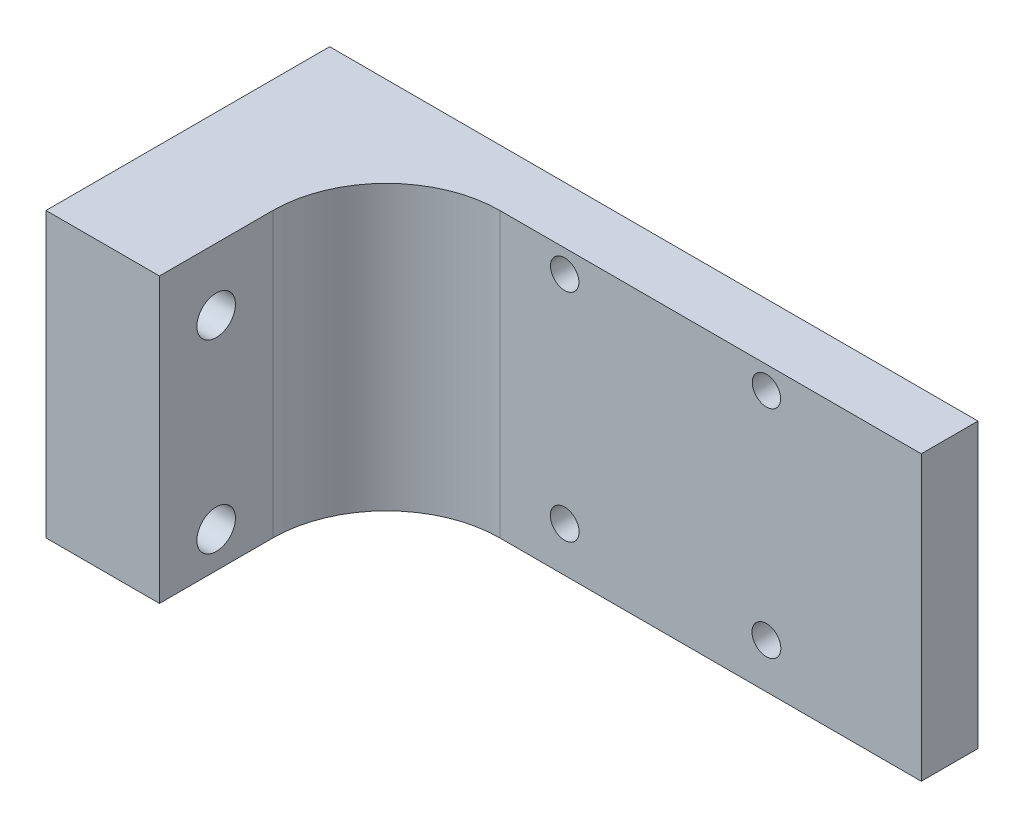
SolidWorks part; units mm, degrees
ref_plane "Front Plane" through (0, 0, 0) normal (0, 0, 1) x (1, 0, 0)
ref_plane "Top Plane" through (0, 0, 0) normal (0, 1, 0) x (1, 0, 0)
ref_plane "Right Plane" through (0, 0, 0) normal (1, 0, 0) x (0, 0, -1)
sketch "Sketch1" plane through (0, 0, 0) normal (0, 0, 1) x (1, 0, 0)
  line L1 (0, 0) -> (57.15, 0)
  line L2 (0, 0) -> (0, -25)
  line L3 (0, -25) -> (57.15, -25)
  line L4 (57.15, 0) -> (57.15, -25)
  dimension "D1" = 57.15
  dimension "D2" = 25
extrude "Boss-Extrude1" add sketch "Sketch1" along normal blind 5
sketch "Sketch2" plane through (0, 0, 5) normal (0, 0, 1) x (1, 0, 0)
  line L0 (0, -2) -> (57.15, -2) construction
  line L1 (0, 0) -> (0, -25) construction
  line L2 (57.15, -25) -> (57.15, 0) construction
  line L3 (37.15, -25) -> (37.15, 0) construction
  line L4 (25.72, -2) -> (25.72, -25) construction
  line L5 (43.5, -2) -> (43.5, -25) construction
  line L6 (17.15, -25) -> (17.15, 0) construction
  line L7 (0, -25) -> (57.15, -25) construction
  line L8 (57.15, 0) -> (0, 0) construction
  line L9 (57.15, -25) -> (57.15, 0) construction
  circle A2 centre (25.72, -2) radius 1.25
  circle A3 centre (43.5, -2) radius 1.25
  circle A4 centre (25.72, -21.05) radius 1.27
  circle A5 centre (43.5, -21.05) radius 1.27
  dimension "D3" = 11.43
  dimension "D4" = 6.35
  dimension "D2" = 20
  dimension "D7" = 2.5
  dimension "D8" = 2.54
  dimension "D9" = 19.05
  dimension "D1" = 2
  dimension "D5" = 19.05
  dimension "D6" = 40
extrude "Cut-Extrude2" cut sketch "Sketch2" against normal through all
sketch "Sketch5" plane through (0, 0, 5) normal (0, 0, 1) x (1, 0, 0)
  line L0 (10, 0) -> (10, -25) construction
  line L1 (57.15, 0) -> (0, 0) construction
  line L2 (0, -25) -> (57.15, -25) construction
  line L4 (0, 0) -> (10, 0)
  line L5 (0, 0) -> (0, -25)
  line L6 (0, -25) -> (10, -25)
  line L7 (10, 0) -> (10, -25)
  dimension "D1" = 10
extrude "Boss-Extrude3" add sketch "Sketch5" along normal blind 20
fillet "Fillet1" radius 10 1 edges at (10, -12.5, 5)
sketch "Sketch6" plane through (10, 0, 0) normal (1, 0, 0) x (0, 0, -1)
  line L0 (-20, -25) -> (-20, 0) construction
  line L1 (-25, -25) -> (-15, -25) construction
  line L2 (-25, 0) -> (-15, 0) construction
  circle A0 centre (-20, -21.8349) radius 1.7
  circle A1 centre (-20, -5.5031) radius 1.7
extrude "Cut-Extrude3" cut sketch "Sketch6" against normal through all
